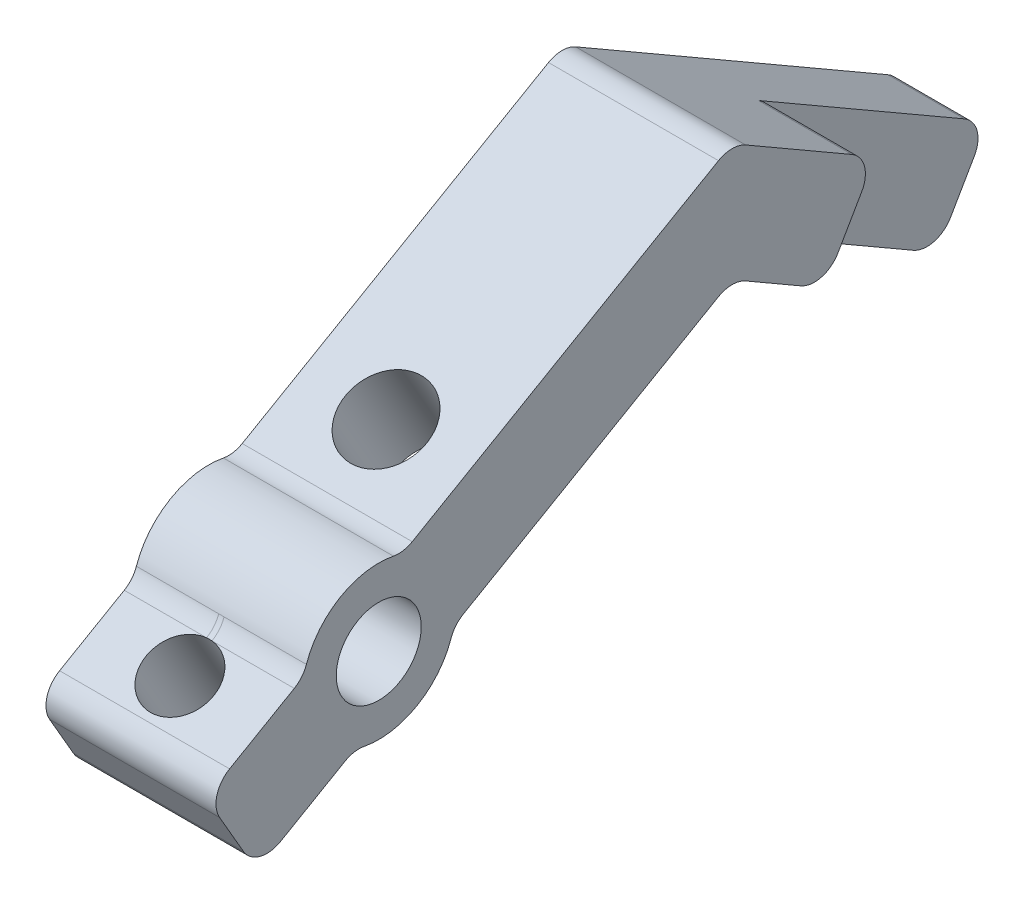
SolidWorks part; units mm, degrees
ref_plane "Front Plane" through (0, 0, 0) normal (0, 0, 1) x (1, 0, 0)
ref_plane "Top Plane" through (0, 0, 0) normal (0, 1, 0) x (1, 0, 0)
ref_plane "Right Plane" through (0, 0, 0) normal (1, 0, 0) x (0, 0, -1)
sketch "Sketch1" plane through (0, 0, 0) normal (1, 0, 0) x (0, 0, -1)
  line L0 (0, 19.05) -> (0, -19.05) construction
  line L1 (0, 19.05) -> (32.9956, 38.1) construction
  line L2 (32.9956, 38.1) -> (63.2415, 20.6375) construction
  line L3 (-8.2489, -14.2875) -> (2.1176, -8.6707) construction
  line L4 (-8.2489, -14.2875) -> (-13.7482, -11.1125) construction
  line L5 (0, 19.05) -> (-8.2489, 14.2875) construction
  line L6 (0, -19.05) -> (-8.2489, -14.2875) construction
  line L7 (10.9985, 25.4) -> (10.9985, -25.4) construction
  line L8 (-8.2489, 14.2875) -> (2.1176, 8.6707) construction
  line L9 (0, 0.3175) -> (-13.3728, 0.3175) construction
  line L10 (32.9956, -38.1) -> (63.2415, -20.6375) construction
  line L11 (0, -0.3175) -> (-13.3728, -0.3175) construction
  line L12 (-8.2489, 14.2875) -> (-13.7482, 11.1125) construction
  line L13 (32.9956, 43.5993) -> (-16.1294, 15.2369)
  line L14 (-16.1294, 15.2369) -> (-11.3669, 6.9881)
  line L15 (-11.3669, 6.9881) -> (32.9956, 32.6007)
  line L17 (0, 0) -> (-16.8904, 0) construction
  line L18 (-11.3669, -6.9881) -> (32.9956, -32.6007)
  line L20 (32.9956, -43.5993) -> (-16.1294, -15.2369)
  line L21 (-16.1294, -15.2369) -> (-11.3669, -6.9881)
  line L22 (32.9956, 43.5993) -> (65.6228, 24.7619)
  line L23 (65.6228, 24.7619) -> (60.8603, 16.5131)
  line L24 (60.8603, 16.5131) -> (32.9956, 32.6007)
  line L25 (32.9956, -43.5993) -> (65.6228, -24.7619)
  line L26 (65.6228, -24.7619) -> (60.8603, -16.5131)
  line L27 (60.8603, -16.5131) -> (32.9956, -32.6007)
  line L28 (0, -19.05) -> (32.9956, -38.1) construction
  circle A2 centre (0, 4.7625) radius 3.175 construction
  circle A3 centre (0, -4.7625) radius 3.175 construction
  arc A4 (2.1176, 8.6707) -> (0, 0.3175) centre (0, 4.7625) cw construction
  arc A5 (2.1176, -8.6707) -> (0, -0.3175) centre (0, -4.7625) ccw construction
  circle A6 centre (28.8658, 0) radius 12.7 construction
  circle A7 centre (0, 19.05) radius 3.9687
  circle A8 centre (0, 19.05) radius 7.1437
  circle A9 centre (0, -19.05) radius 7.1437
  circle A10 centre (0, -19.05) radius 3.9687
  point P0 (0, 0)
  dimension "D10" = 6.35
  dimension "D13" = 1.27
  dimension "D15" = 9.525
  dimension "D16" = 25.4
  dimension "D17" = 7.9375
  dimension "D18" = 14.2875
  dimension "D1" = 38.1
  dimension "D3" = 120
  dimension "D4" = 34.925
  dimension "D5" = 38.1
  dimension "D7" = 9.525
  dimension "D8" = 12.7
  dimension "D11" = 4.7625
  dimension "D14" = 6.35
  dimension "D19" = 30
extrude "Boss-Extrude1" add sketch "Sketch1" along normal blind 15.875 contours A8 L13 L14 L15 | L13 A8 | L15 A8 | A8 L15 L24 L23 L22 L13 | L13 A8 L15 A7
sketch "Sketch2" plane through (0, 18.4119, 10.6301) normal (0, 0.866, 0.5) x (1, 0, 0)
  line L0 (15.875, 5.5562) -> (15.875, 13.4937) construction
  line L1 (15.875, 5.5562) -> (15.875, 13.4937)
  line L2 (15.875, -6.35) -> (0, -6.35) construction
  circle A0 centre (7.9375, 0) radius 3.175
  circle A1 centre (7.9375, 22.225) radius 3.81
  point P4 (15.875, 9.525)
  point P5 (7.9375, -6.35)
  dimension "D1" = 6.35
  dimension "D3" = 7.62
  dimension "D2" = 9.525
  dimension "D4" = 12.7
extrude "Cut-Extrude1" cut sketch "Sketch2" against normal up to surface (9.525 mm away) contours A0 | A1 up to face at (7.9375, 25.0943, -19.994)
ref_plane "Plane2" through (15.875, 0, 0) normal (1, 0, 0) x (0, 0, -1)
sketch "Sketch3" plane through (15.875, 0, 0) normal (1, 0, 0) x (0, 0, -1)
  line L0 (65.6228, 24.7619) -> (60.8603, 16.5131) construction
  line L1 (32.9956, 43.5993) -> (65.6228, 24.7619) construction
  line L2 (60.8603, 16.5131) -> (32.9956, 32.6007) construction
  line L3 (65.6228, 24.7619) -> (60.8603, 16.5131)
  line L4 (46.3753, 35.8744) -> (65.6228, 24.7619)
  line L5 (60.8603, 16.5131) -> (41.6128, 27.6256)
  line L7 (41.6128, 27.6256) -> (46.3753, 35.8744)
  dimension "D1" = 22.225
extrude "Cut-Extrude2" cut sketch "Sketch3" against normal blind 8.7312
sketch "Sketch4" plane through (0, 0, 0) normal (-1, 0, 0) x (0, 0, 1)
  line L0 (-41.6128, 27.6256) -> (-46.3753, 35.8744) construction
  line L1 (-65.6228, 24.7619) -> (-60.8603, 16.5131) construction
  line L2 (-60.8603, 16.5131) -> (-41.6128, 27.6256) construction
  line L3 (-41.6128, 27.6256) -> (-46.3753, 35.8744)
  line L4 (-65.6228, 24.7619) -> (-60.8603, 16.5131)
  line L5 (-60.8603, 16.5131) -> (-41.6128, 27.6256)
  line L6 (-46.3753, 35.8744) -> (-65.6228, 24.7619) construction
  line L7 (-46.3753, 35.8744) -> (-65.6228, 24.7619)
fillet "Fillet1" radius 2.54 12 edges at (7.9375, 15.2369, 16.1294) (7.9375, 6.9881, 11.3669) (7.9375, 17.5879, -6.9925) (7.9375, 12.2632, 2.23) (7.9375, 20.5121, 6.9925) (7.9375, 25.8368, -2.23) (7.9375, 43.5993, -32.9956) (7.9375, 32.6007, -32.9956) (11.5094, 35.8744, -46.3753) (11.5094, 27.6256, -41.6128) (3.5719, 16.5131, -60.8603) (3.5719, 24.7619, -65.6228)
